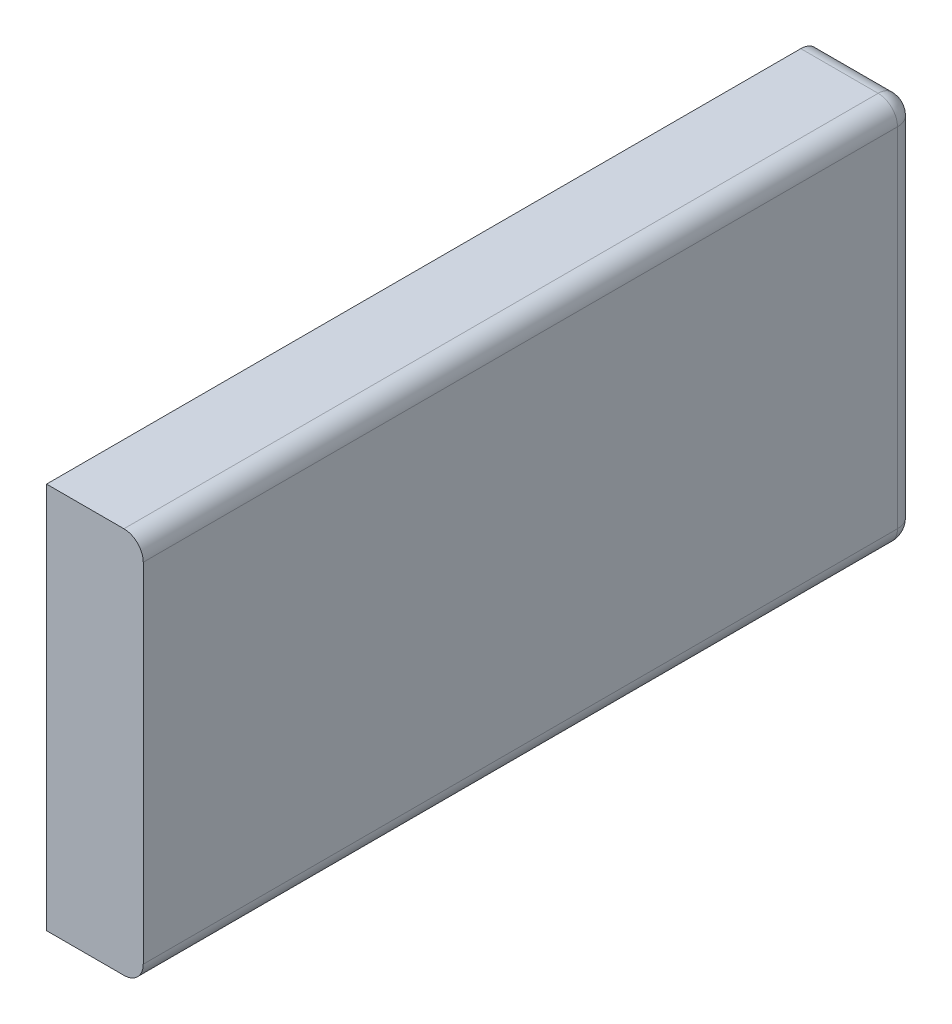
SolidWorks part; units mm, degrees
ref_plane "Front Plane" through (0, 0, 0) normal (0, 0, 1) x (1, 0, 0)
ref_plane "Top Plane" through (0, 0, 0) normal (0, 1, 0) x (1, 0, 0)
ref_plane "Right Plane" through (0, 0, 0) normal (1, 0, 0) x (0, 0, -1)
sketch "Sketch2" plane through (0, 0, 0) normal (0, 1, 0) x (1, 0, 0)
  line L0 (0, 0) -> (0, 101.6)
  line L1 (0, 101.6) -> (12.7, 101.6)
  line L2 (12.7, 101.6) -> (12.7, 0)
  line L3 (12.7, 0) -> (0, 0)
  dimension "D1" = 12.7
  dimension "D2" = 101.6
extrude "Boss-Extrude3" add sketch "Sketch2" along normal blind 50.8
fillet "Fillet2" radius 2.54 5 edges at (12.7, 25.4, -101.6) (12.7, 0, -50.8) (12.7, 50.8, -50.8) (6.35, 50.8, -101.6) (6.35, 0, -101.6)
